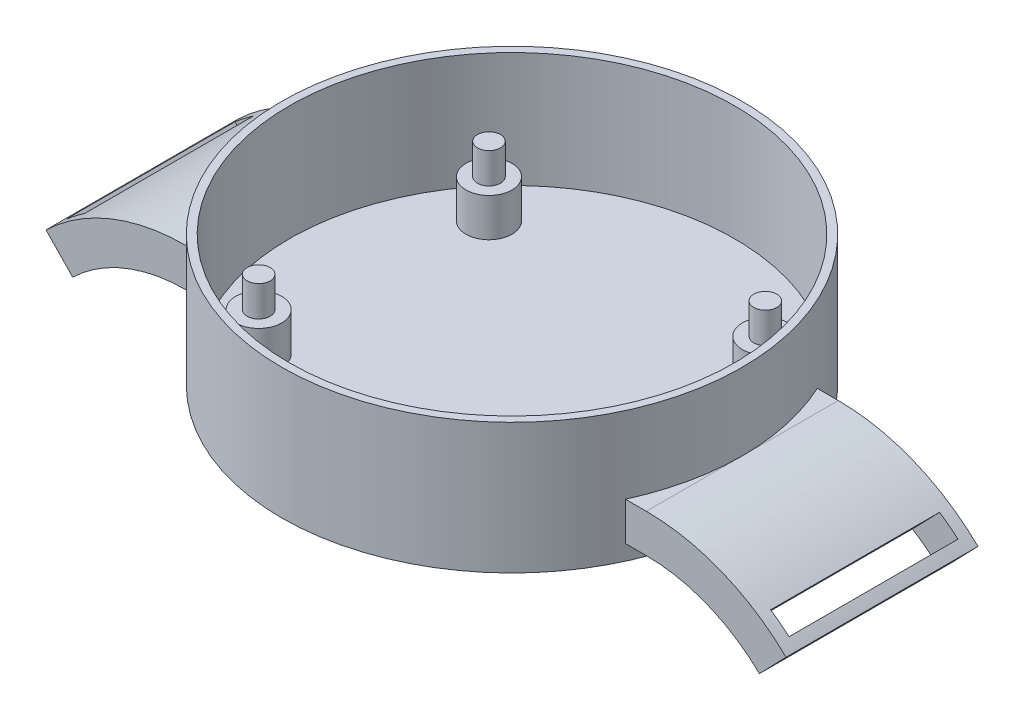
SolidWorks part; units mm, degrees
ref_plane "Front Plane" through (0, 0, 0) normal (0, 0, 1) x (1, 0, 0)
ref_plane "Top Plane" through (0, 0, 0) normal (0, 1, 0) x (1, 0, 0)
ref_plane "Right Plane" through (0, 0, 0) normal (1, 0, 0) x (0, 0, -1)
sketch "Sketch1" plane through (0, 0, 0) normal (0, 1, 0) x (1, 0, 0)
  circle A0 centre (0, 0) radius 30
extrude "Boss-Extrude1" add sketch "Sketch1" along normal blind 17
sketch "Sketch2" plane through (0, 17, 0) normal (0, 1, 0) x (1, 0, 0)
  circle A0 centre (0, 0) radius 29
extrude "Cut-Extrude1" cut sketch "Sketch2" against normal blind 15
sketch "Sketch3" plane through (0, 2, 0) normal (0, 1, 0) x (1, 0, 0)
  circle A0 centre (-18, 15) radius 3
  circle A1 centre (-18, -15) radius 3
  circle A2 centre (18, -15) radius 3
  circle A3 centre (18, 15) radius 3
  point P0 (0, 0)
extrude "Boss-Extrude5" add sketch "Sketch3" along normal blind 5
sketch "Sketch4" plane through (0, 7, 0) normal (0, 1, 0) x (1, 0, 0)
  circle A1 centre (-18, 15) radius 1.5
  circle A2 centre (-18, -15) radius 1.5
  circle A3 centre (18, 15) radius 1.5
  circle A4 centre (18, -15) radius 1.5
extrude "Boss-Extrude6" add sketch "Sketch4" along normal blind 4
ref_plane "Plane1" through (-30, 0, 0) normal (-1, 0, 0) x (0, 0, 1)
sketch "Sketch6" plane through (-30, 0, 0) normal (-1, 0, 0) x (0, 0, 1)
  line L0 (-30, 0) -> (30, 0) construction
  line L1 (-12.5, 7) -> (12.5, 7)
  line L2 (-12.5, 7) -> (-12.5, 2)
  line L3 (-12.5, 2) -> (12.5, 2)
  line L4 (12.5, 7) -> (12.5, 2)
  line L5 (-12.5, 7) -> (12.5, 2) construction
  line L6 (-12.5, 2) -> (12.5, 7) construction
  point P0 (0, 4.5)
  point P8 (0, 0)
  dimension "D1" = 25
  dimension "D2" = 5
  dimension "D3" = 2
  dimension "D4" = 12.5
sketch "Sketch7" plane through (0, 0, 0) normal (0, 0, 1) x (1, 0, 0)
  line L0 (-30, 2) -> (-30, 7) construction
  line L1 (-30, 4.5) -> (-17.5787, 4.5) construction
  arc A0 (-30, 4.5) -> (-46.4617, -2.1565) centre (-30, -19.1835) ccw
  point P3 (-45.5972, -1.9797)
  point P7 (-45.9092, -3.3152)
  point P8 (-45.42, 0)
  point P9 (0, 0)
  point P10 (0, 0)
  point P11 (0, 0)
  point P12 (-46.4617, -2.1565)
extrude "Boss-Extrude7" add sketch "Sketch6" against normal up to surface (2.7282 mm away) contours L1 L4 L3 L2
sketch "Sketch9" plane through (-30, 0, 0) normal (-1, 0, 0) x (0, 0, 1)
  line L1 (-12.5, 7) -> (12.5, 7)
  line L2 (-12.5, 7) -> (-12.5, 2)
  line L3 (-12.5, 2) -> (12.5, 2)
  line L4 (12.5, 7) -> (12.5, 2)
sweep "Sweep1" add profiles "Sketch9" path "Sketch7"
ref_plane "Plane2" through (-23.1068, 23.9004, 0) normal (-0.6951, 0.7189, 0) x (0.7189, 0.6951, 0)
sketch "Sketch10" plane through (-23.1068, 23.9004, 0) normal (-0.6951, 0.7189, 0) x (0.7189, 0.6951, 0)
  line L0 (-34.9021, -12.5) -> (-16.7027, -12.5) construction
  line L1 (-33.4021, -11) -> (-30.4021, -11)
  line L2 (-33.4021, -11) -> (-33.4021, 11)
  line L3 (-33.4021, 11) -> (-30.4021, 11)
  line L4 (-30.4021, -11) -> (-30.4021, 11)
  line L5 (-34.9021, -12.5) -> (-34.9021, 12.5) construction
  dimension "D1" = 22
  dimension "D2" = 1.5
  dimension "D3" = 1.5
  dimension "D4" = 3
extrude "Cut-Extrude2" cut sketch "Sketch10" against normal blind 10
pattern_circular "CirPattern1" count 2 every 180 about axis through (0, 0, 0) along (0, 1, 0) of "Sweep1", "Boss-Extrude7", "Cut-Extrude2"
